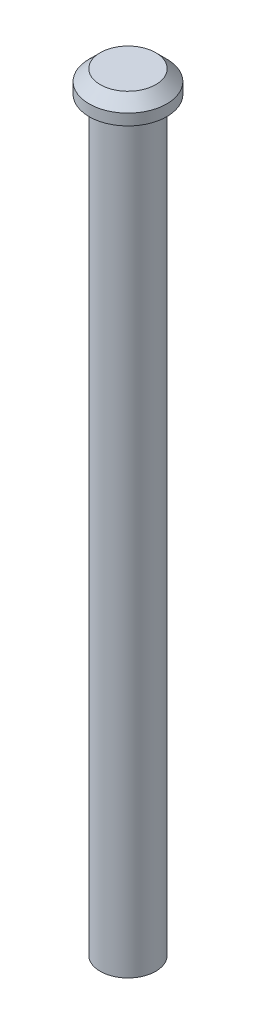
SolidWorks part; units mm, degrees
ref_plane "Front Plane" through (0, 0, 0) normal (0, 0, 1) x (1, 0, 0)
ref_plane "Top Plane" through (0, 0, 0) normal (0, 1, 0) x (1, 0, 0)
ref_plane "Right Plane" through (0, 0, 0) normal (1, 0, 0) x (0, 0, -1)
sketch "Sketch1" plane through (0, 0, 0) normal (0, 1, 0) x (1, 0, 0)
  circle A0 centre (0, 0) radius 2.5
  dimension "D1" = 5
extrude "Boss-Extrude1" add sketch "Sketch1" along normal blind 67.21
sketch "Sketch2" plane through (0, 67.21, 0) normal (0, 1, 0) x (1, 0, 0)
  circle A0 centre (0, 0) radius 3.5
  dimension "D1" = 7
extrude "Boss-Extrude2" add sketch "Sketch2" along normal blind 2
chamfer "Chamfer1" distance 1 angle 45 1 edges at (0, 69.21, 3.5)
sketch "Sketch3" plane through (0, 0, 0) normal (0, -1, 0) x (1, 0, 0)
  circle A0 centre (0, 0) radius 1.5
  dimension "D1" = 3
extrude "Cut-Extrude1" cut sketch "Sketch3" against normal blind 5
